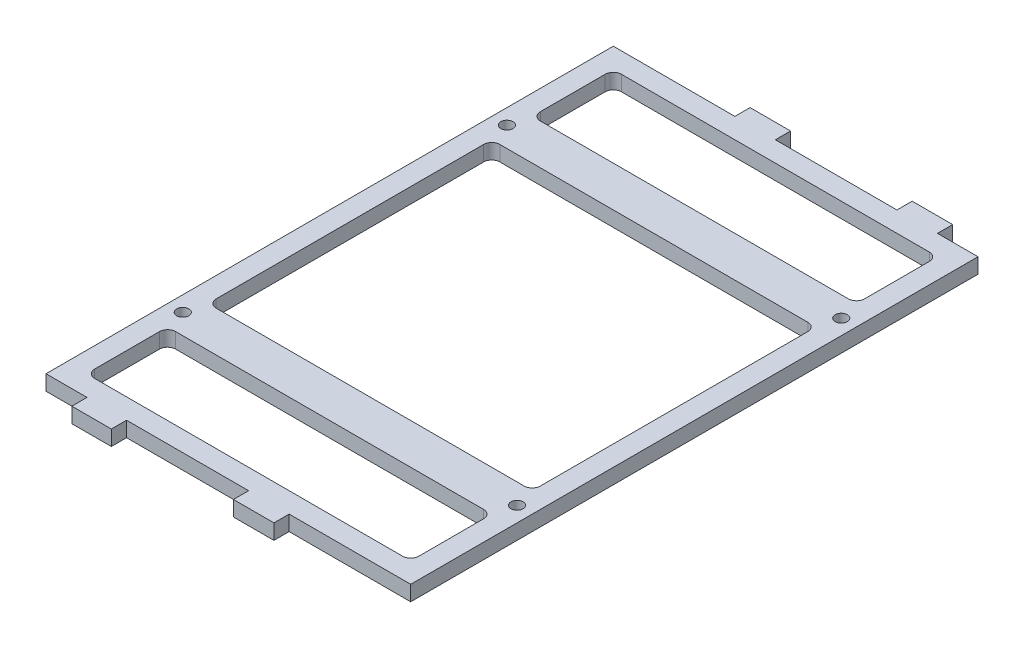
SolidWorks part; units mm, degrees
material "6061-T6 (SS)"
ref_plane "Front Plane" through (0, 0, 0) normal (0, 0, 1) x (1, 0, 0)
ref_plane "Top Plane" through (0, 0, 0) normal (0, 1, 0) x (1, 0, 0)
ref_plane "Right Plane" through (0, 0, 0) normal (1, 0, 0) x (0, 0, -1)
sketch "Sketch1" plane through (0, 0, 0) normal (0, 1, 0) x (1, 0, 0)
  line L0 (50.8, 82.55) -> (-50.8, 82.55)
  line L1 (57.15, 88.9) -> (-57.15, 88.9)
  line L2 (57.15, 88.9) -> (57.15, -88.9)
  line L3 (57.15, -88.9) -> (-57.15, -88.9)
  line L4 (-57.15, 88.9) -> (-57.15, -88.9)
  line L5 (57.15, 88.9) -> (-57.15, -88.9) construction
  line L6 (57.15, -88.9) -> (-57.15, 88.9) construction
  line L7 (-50.8, 82.55) -> (-50.8, -82.55)
  line L8 (50.8, -82.55) -> (-50.8, -82.55)
  line L9 (50.8, 82.55) -> (50.8, -82.55)
  point P0 (0, 0)
  dimension "D1" = 114.3
  dimension "D2" = 177.8
  dimension "D3" = 6.35
extrude "Boss-Extrude1" add sketch "Sketch1" along normal blind 4.7625
sketch "Sketch2" plane through (0, 0, 88.9) normal (0, 0, 1) x (1, 0, 0)
  line L0 (-57.15, 2.3813) -> (57.15, 2.3813) construction
  line L1 (-57.15, 4.7625) -> (-57.15, 0) construction
  line L2 (57.15, 4.7625) -> (57.15, 0) construction
  line L3 (-57.15, 0) -> (57.15, 0) construction
  line L4 (-31.9066, 4.7625) -> (-44.2934, 4.7625)
  line L5 (-31.9066, 4.7625) -> (-31.9066, 0)
  line L6 (-31.9066, 0) -> (-44.2934, 0)
  line L7 (-44.2934, 4.7625) -> (-44.2934, 0)
  line L8 (-31.9066, 4.7625) -> (-44.2934, 0) construction
  line L9 (-31.9066, 0) -> (-44.2934, 4.7625) construction
  line L11 (19.05, 4.7625) -> (6.35, 4.7625)
  line L12 (19.05, 4.7625) -> (19.05, 0)
  line L13 (19.05, 0) -> (6.35, 0)
  line L14 (6.35, 4.7625) -> (6.35, 0)
  line L15 (19.05, 4.7625) -> (6.35, 0) construction
  line L16 (19.05, 0) -> (6.35, 4.7625) construction
  point P6 (-38.1, 2.3813)
  point P13 (12.7, 2.3813)
  dimension "D1" = 19.05
  dimension "D2" = 50.8
  dimension "D3" = 12.7
extrude "Boss-Extrude2" add sketch "Sketch2" along normal blind 4.7625
sketch "Sketch3" plane through (0, 0, -88.9) normal (0, 0, -1) x (-1, 0, 0)
  line L0 (-57.15, 2.3813) -> (57.15, 2.3813) construction
  line L1 (-57.15, 4.7625) -> (-57.15, 0) construction
  line L2 (57.15, 4.7625) -> (57.15, 0) construction
  line L3 (-57.15, 0) -> (57.15, 0) construction
  line L4 (-31.75, 4.7625) -> (-44.45, 4.7625)
  line L5 (-31.75, 4.7625) -> (-31.75, 0)
  line L6 (-31.75, 0) -> (-44.45, 0)
  line L7 (-44.45, 4.7625) -> (-44.45, 0)
  line L8 (-31.75, 4.7625) -> (-44.45, 0) construction
  line L9 (-31.75, 0) -> (-44.45, 4.7625) construction
  line L11 (19.05, 4.7625) -> (6.35, 4.7625)
  line L12 (19.05, 4.7625) -> (19.05, 0)
  line L13 (19.05, 0) -> (6.35, 0)
  line L14 (6.35, 4.7625) -> (6.35, 0)
  line L15 (19.05, 4.7625) -> (6.35, 0) construction
  line L16 (19.05, 0) -> (6.35, 4.7625) construction
  point P6 (-38.1, 2.3812)
  point P13 (12.7, 2.3812)
  dimension "D1" = 12.7
  dimension "D2" = 12.7
  dimension "D3" = 19.05
  dimension "D4" = 50.8
extrude "Boss-Extrude3" add sketch "Sketch3" along normal blind 4.7625
fillet "Fillet1" radius 2.54 4 edges at (50.8, 2.3813, 82.55) (50.8, 2.3813, -82.55) (-50.8, 2.3813, -82.55) (-50.8, 2.3813, 82.55)
sketch "Sketch4" plane through (0, 4.7625, 0) normal (0, 1, 0) x (1, 0, 0)
  line L0 (-57.15, 50.8) -> (57.15, 50.8) construction
  line L1 (-57.15, 88.9) -> (-57.15, -88.9) construction
  line L2 (57.15, -88.9) -> (57.15, 88.9) construction
  line L3 (-57.15, -50.8) -> (57.15, -50.8) construction
  line L5 (57.15, -44.45) -> (-57.15, -44.45)
  line L6 (57.15, -44.45) -> (57.15, -57.15)
  line L7 (57.15, -57.15) -> (-57.15, -57.15)
  line L8 (-57.15, -44.45) -> (-57.15, -57.15)
  line L9 (57.15, -44.45) -> (-57.15, -57.15) construction
  line L10 (57.15, -57.15) -> (-57.15, -44.45) construction
  line L11 (57.15, 57.15) -> (-57.15, 57.15)
  line L12 (57.15, 57.15) -> (57.15, 44.45)
  line L13 (57.15, 44.45) -> (-57.15, 44.45)
  line L14 (-57.15, 57.15) -> (-57.15, 44.45)
  line L15 (57.15, 57.15) -> (-57.15, 44.45) construction
  line L16 (57.15, 44.45) -> (-57.15, 57.15) construction
  point P8 (0, -50.8)
  point P13 (0, 50.8)
  dimension "D1" = 12.7
  dimension "D2" = 12.7
  dimension "D3" = 50.8
  dimension "D4" = 50.8
extrude "Boss-Extrude4" add sketch "Sketch4" against normal blind 4.7625
hole_wizard "#6 Clearance Hole1" positions "Sketch6" profile "Sketch5" hole size "#6" standard "Ansi Inch"
sketch "Sketch6" plane through (0, 4.7625, 0) normal (0, 1, 0) x (-1, 0, 0)
  line L0 (57.15, -50.8) -> (-57.15, -50.8) construction
  line L1 (57.15, -88.9) -> (57.15, 88.9) construction
  line L2 (-57.15, 88.9) -> (-57.15, -88.9) construction
  line L4 (57.15, 50.8) -> (-57.15, 50.8) construction
  point P0 (52.3875, -50.8)
  point P1 (-52.3875, -50.8)
  point P3 (52.3875, 50.8)
  point P5 (-52.3875, 50.8)
  dimension "D1" = 50.8
  dimension "D2" = 50.8
  dimension "D3" = 4.7625
  dimension "D4" = 4.7625
  dimension "D5" = 4.7625
  dimension "D6" = 4.7625
sketch "Sketch5" plane through (-52.3875, 4.7625, -50.8) normal (1, 0, 0) x (0, 0, 1)
  line L0 (0, 0) -> (0, 26.5408)
  line L1 (0, 26.5408) -> (1.8986, 25.4)
  line L2 (1.8986, 25.4) -> (1.8986, 0)
  line L5 (1.8986, 0) -> (0, 0)
  line L10 (0, 26.5408) -> (-1.8986, 25.4) construction
  line L11 (0, -6.35) -> (0, 107.95) construction
  dimension "Hole Dia." = 3.7973
  dimension "Hole Depth" = 25.4
  dimension "Drill Angle" = 118
fillet "Fillet2" radius 2.54 8 edges at (50.8, 2.3813, -57.15) (-50.8, 2.3813, -57.15) (50.8, 2.3813, 57.15) (-50.8, 2.3813, 57.15) (50.8, 2.3813, -44.45) (-50.8, 2.3813, -44.45) (50.8, 2.3813, 44.45) (-50.8, 2.3813, 44.45)
